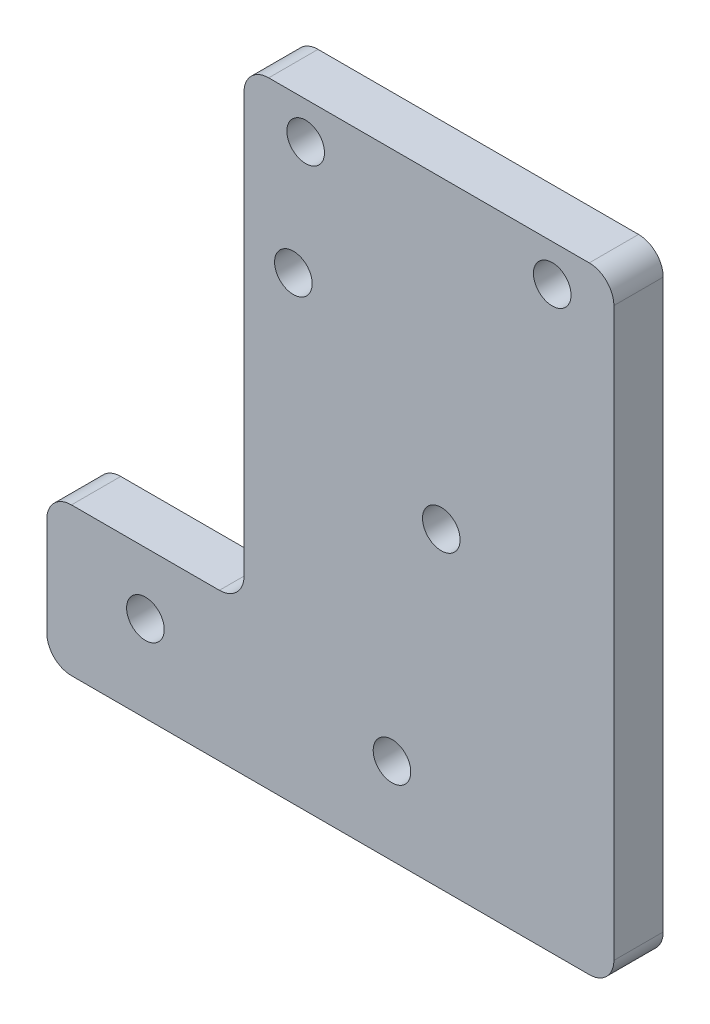
SolidWorks part; units mm, degrees
material "Thornel Mat VMA"
ref_plane "前视基准面" through (0, 0, 0) normal (0, 0, 1) x (1, 0, 0)
ref_plane "上视基准面" through (0, 0, 0) normal (0, 1, 0) x (1, 0, 0)
ref_plane "右视基准面" through (0, 0, 0) normal (1, 0, 0) x (0, 0, -1)
other "Configuration Table"
sketch "草图2" plane through (0, 0, 0) normal (0, 0, 1) x (1, 0, 0)
  line L1 (-15, -15) -> (15, -15)
  line L2 (-15, -15) -> (-15, 15)
  line L3 (-15, 15) -> (15, 15)
  line L4 (15, -15) -> (15, 15)
  line L5 (-15, -15) -> (15, 15) construction
  line L6 (-15, 15) -> (15, -15) construction
  point P0 (0, 0)
  dimension "D1" = 30
  dimension "D2" = 30
extrude "凸台-拉伸1" add sketch "草图2" along normal mid plane 4
sketch "草图3" plane through (0, 0, 2) normal (0, 0, 1) x (1, 0, 0)
  line L5 (15, -15) -> (15, 15) construction
  line L6 (-15, -15) -> (15, -15)
  line L7 (-15, -15) -> (-15, -35)
  line L8 (-15, -35) -> (15, -35)
  line L9 (15, -15) -> (15, -35)
  dimension "D1" = 20
extrude "凸台-拉伸2" add sketch "草图3" against normal up to surface (4 mm away) up to face at (0, 0, -2)
sketch "草图4" plane through (0, 0, 2) normal (0, 0, 1) x (1, 0, 0)
  arc A0 (-11.9946, 3.4228) -> (-11, 0.8) centre (-11, 2.3) ccw construction
  arc A1 (0.0054, -8.5772) -> (1, -11.2) centre (1, -9.7) ccw construction
  arc A2 (-11.9946, 3.4228) -> (-11, 0.8) centre (-11, 2.3) ccw
  arc A3 (0.0054, -8.5772) -> (1, -11.2) centre (1, -9.7) ccw
sketch "草图5" plane through (0, 0, 2) normal (0, 0, 1) x (1, 0, 0)
  circle A0 centre (10, 12) radius 1.5 construction
  circle A1 centre (-10, 12) radius 1.5 construction
  circle A2 centre (10, 12) radius 1.5
  circle A3 centre (-10, 12) radius 1.5
sketch "草图6" plane through (0, 0, 2) normal (0, 0, 1) x (1, 0, 0)
  circle A0 centre (1, -9.7) radius 1.525
  circle A1 centre (-11, 2.3) radius 1.525
  circle A2 centre (-10, 12) radius 1.525
  circle A3 centre (10, 12) radius 1.525
  dimension "D1" = 3.05
extrude "切除-拉伸1" cut sketch "草图6" against normal blind 80
fillet "圆角1" [suppressed] radius 2
sketch "草图7" plane through (0, 0, 2) normal (0, 0, 1) x (1, 0, 0)
  line L0 (-15, -35) -> (-31, -35)
  line L1 (-31, -35) -> (-31, -23)
  line L2 (-31, -23) -> (-15, -23)
  line L3 (-15, 15) -> (-15, -35) construction
  line L4 (-15, -23) -> (-15, -35)
  line L5 (15, -35) -> (15, 15) construction
  dimension "D1" = 46
  dimension "D2" = 12
extrude "凸台-拉伸3" add sketch "草图7" against normal up to surface (4 mm away) up to face at (-0.525, -9.7, -2)
sketch "草图8" plane through (0, 0, -2) normal (0, 0, -1) x (-1, 0, 0)
  circle A0 centre (23, -28) radius 1.5 construction
  circle A1 centre (3, -28) radius 1.5 construction
  circle A2 centre (23, -28) radius 1.5
  circle A3 centre (3, -28) radius 1.5
sketch "草图9" plane through (0, 0, -2) normal (0, 0, -1) x (-1, 0, 0)
  circle A0 centre (3, -28) radius 1.525
  circle A1 centre (23, -28) radius 1.525
  dimension "D1" = 3.05
extrude "切除-拉伸2" cut sketch "草图9" against normal blind 4
fillet "圆角2" radius 2 6 edges at (15, 15, 0) (-15, 15, 0) (-15, -23, 0) (15, -35, 0) (-31, -35, 0) (-31, -23, 0)
